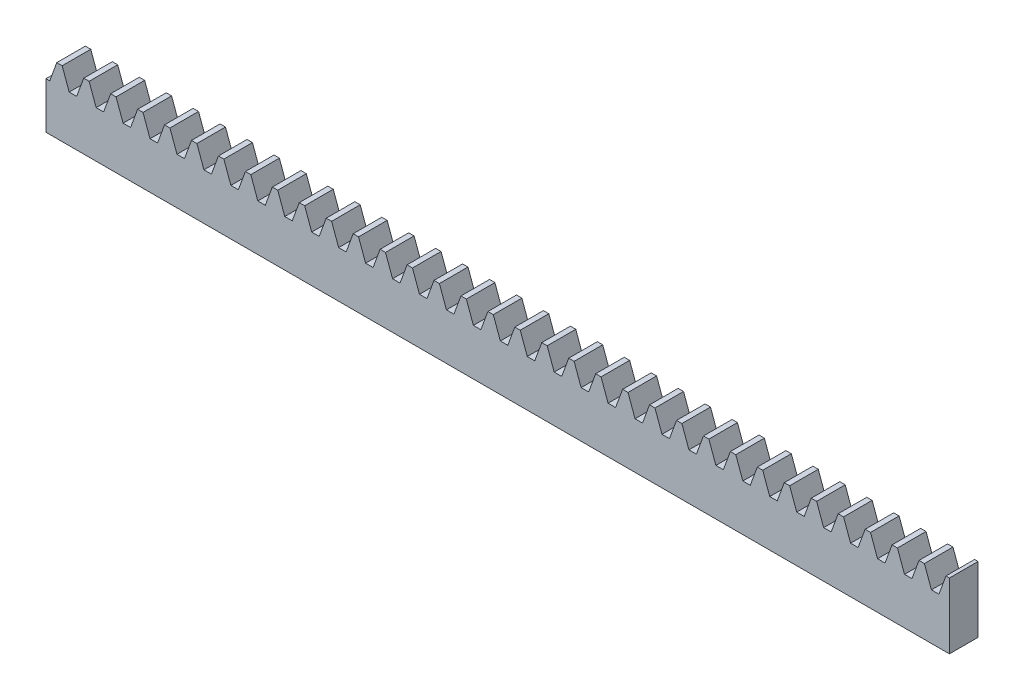
SolidWorks part; units mm, degrees
ref_plane "Plane1" through (0, 0, 0) normal (0, 0, 1) x (1, 0, 0)
ref_plane "Plane2" through (0, 0, 0) normal (0, 1, 0) x (1, 0, 0)
ref_plane "Plane3" through (0, 0, 0) normal (1, 0, 0) x (0, 0, -1)
sketch "HoldingSke" plane through (0, 0, 0) normal (0, 1, 0) x (1, 0, 0)
  line L0 (0, 0) -> (0.0928, 0.6602)
  line L1 (-15, 0) -> (100, 0) construction
  line L2 (0, 0) -> (-2.1039, 2.3779)
  line L3 (0, 0) -> (-11.863, 4.5341)
  line L4 (0, 0) -> (7.0742, 4.9534)
  line L5 (0, 0) -> (-23.7986, -8.8762)
  line L6 (0, 0) -> (-10.5278, -7.1032)
  line L9 (-71.009, 38.7566) -> (77.4625, 92.7958)
  line L10 (-76.2, 3.8779) -> (-66.2, 3.8779)
  line L11 (0, 0) -> (-5, 0)
  line L12 (-76.2, 101.6) -> (-76.147, 101.6)
  line L13 (24.9733, 27.94) -> (52.9518, 28.4284)
  line L14 (24.9733, 27.94) -> (24.9743, 27.94)
  line L15 (24.9733, 27.94) -> (100.4006, 29.5858)
  circle A0 centre (0, 0) radius 19.05
  circle A1 centre (0, 0) radius 5
  circle A2 centre (0, 0) radius 12.7
  dimension "MPH" = 10
  dimension "Diameter" = 38.1
  dimension "Num_teeth" = 35
  dimension "Pitch" = 0.6667
  dimension "Width" = 5
  dimension "Show_teeth" = 998
  dimension "Thickness" = 12.7
  dimension "Ap" = 20
  dimension "Pitch_height" = 10
  dimension "Backlash" = 0.053
  dimension "Addendum_fac" = 1
  dimension "Dedendum_fac" = 1.25
  dimension "Clearance_fac" = 0.25
  dimension "Dedendum_add" = 0.001
  dimension "Length" = 158
  dimension "Module" = 1.5
sketch "BlankSke" plane through (0, 0, 0) normal (0, 0, 1) x (1, 0, 0)
  line L1 (0, 0) -> (158, 0)
  line L2 (0, 0) -> (0, 11.5)
  line L3 (0, 11.5) -> (158, 11.5)
  line L4 (158, 0) -> (158, 11.5)
  dimension "Length" = 158
  dimension "Blank_height" = 11.5
extrude "Blank" add sketch "BlankSke" against normal blind 5
sketch "TooCutSkeIll" plane through (0, 0, 0) normal (0, 0, 1) x (1, 0, 0)
  line L0 (-1.8687, 11.4605) -> (-0.7447, 8.3724)
  line L1 (-0.3914, 8.125) -> (0.3914, 8.125)
  line L2 (0.7447, 8.3724) -> (1.8687, 11.4605)
  line L3 (158, 11.5) -> (0, 11.5) construction
  line L4 (0, 0) -> (0, 64.897) construction
  line L5 (-13.208, 10) -> (12.954, 10) construction
  line L6 (0, 0) -> (158, 0) construction
  line L7 (1.3371, 10) -> (1.3371, 48.7463) construction
  line L8 (-1.3371, 10) -> (-1.3371, 48.7463) construction
  line L9 (1.9251, 11.5) -> (1.9251, 11.5254)
  line L10 (-1.9251, 11.5) -> (-1.9251, 11.5254)
  line L11 (-1.9251, 11.5254) -> (1.9251, 11.5254)
  arc A0 (0.3914, 8.125) -> (0.7447, 8.3724) centre (0.3914, 8.501) ccw
  arc A1 (-0.7447, 8.3724) -> (-0.3914, 8.125) centre (-0.3914, 8.501) ccw
  arc A2 (1.9251, 11.5) -> (1.8687, 11.4605) centre (1.9251, 11.44) ccw
  arc A3 (-1.8687, 11.4605) -> (-1.9251, 11.5) centre (-1.9251, 11.44) ccw
  dimension "Root_fillet" = 0.376
  dimension "Break_rad" = 0.06
  dimension "Pitch_height" = 10
  dimension "Gap_width" = 2.6742
  dimension "Dedendum" = 1.875
  dimension "Addendum_plus" = 1.5254
  dimension "Pressure_angle" = 20
extrude "ToothCutIll" [suppressed] cut sketch "TooCutSkeIll" against normal through all
sketch "TooCutSkeSim" plane through (0, 0, 0) normal (0, 0, 1) x (1, 0, 0)
  line L0 (0.6547, 8.125) -> (-0.6547, 8.125)
  line L1 (1.8923, 11.5254) -> (0.6547, 8.125)
  line L2 (0, 17.4625) -> (0, 53.467) construction
  line L3 (1.8923, 11.5254) -> (-1.8923, 11.5254)
  line L6 (-1.8923, 11.5254) -> (-0.6547, 8.125)
  line L9 (-1.3371, 10) -> (1.3371, 10) construction
  line L10 (0, 0) -> (158, 0) construction
  line L11 (1.3371, 10) -> (1.3371, 53.467) construction
  line L12 (-1.3371, 10) -> (-1.3371, 53.467) construction
  dimension "Pitch_height" = 10
  dimension "Pressure_angle" = 20
  dimension "Gap_width" = 2.6742
  dimension "Dedendum" = 1.875
  dimension "Addendum_plus" = 1.5254
extrude "ToothCutSim" cut sketch "TooCutSkeSim" against normal through all
pattern_linear "TeethCuts" count 34 spacing 4.7124 along (1, 0, 0) of "ToothCutIll", "ToothCutSim"
equation "' \"Module@HoldingSke\" = 6.35"
equation "' \"Num_teeth@HoldingSke\" = 12"
equation "' \"Ap@HoldingSke\" =  20"
equation "' \"Width@HoldingSke\" = 0.25 * 25.4"
equation "' \"Show_teeth@HoldingSke\" = 500"
equation "' \"Backlash@HoldingSke\" = 0.009 * 25.4"
equation "' \"Addendum_fac@HoldingSke\" = 1.0"
equation "' \"Dedendum_fac@HoldingSke\" = 1.25"
equation "' \"Dedendum_add@HoldingSke\" = 0.00005 * 25.4"
equation "' \"Clearance_fac@HoldingSke\" = 0.25"
equation "' \"Pitch_height@HoldingSke\" = 1 * 25.4"
equation "' \"Length@HoldingSke\" = 4.71 * 25.4"
equation "\"Pitch@HoldingSke\" = 1 / \"Module@HoldingSke\""
equation "\"MPH@HoldingSke\" = \"Dedendum_fac@HoldingSke\" / \"Pitch@HoldingSke\" + 2 * \"Dedendum_add@HoldingSke\" + 0.002 * 25.4"
equation "\"MPH@HoldingSke\" = ((sgn( \"MPH@HoldingSke\" - \"Pitch_height@HoldingSke\")+1)*( \"MPH@HoldingSke\" - \"Pitch_height@HoldingSke\"))/2 + \"Pitch_height@HoldingSke\""
equation "\"Blank_height@BlankSke\" = \"Pitch_height@HoldingSke\" + \"Addendum_fac@HoldingSke\"  / \"Pitch@HoldingSke\" "
equation "\"Length@BlankSke\" =  \"Length@HoldingSke\""
equation "\"Face_width@Blank\" = \"Width@HoldingSke\""
equation "\"Pressure_angle@TooCutSkeIll\" = \"Ap@HoldingSke\""
equation "\"Addendum_plus@TooCutSkeIll\" =  \"Addendum_fac@HoldingSke\"  / \"Pitch@HoldingSke\" + 0.001 *25.4"
equation "\"Dedendum@TooCutSkeIll\" = \"Dedendum_fac@HoldingSke\"  / \"Pitch@HoldingSke\""
equation "\"Pitch_height@TooCutSkeIll\" =  \"MPH@HoldingSke\""
equation "\"Gap_width@TooCutSkeIll\" = 3.14159265 / 2 / \"Pitch@HoldingSke\" + 6 * \"Backlash@HoldingSke\""
equation "\"Pressure_angle@TooCutSkeSim\" = \"Ap@HoldingSke\""
equation "\"Addendum_plus@TooCutSkeSim\" =  \"Addendum_fac@HoldingSke\"  / \"Pitch@HoldingSke\" + 0.001 * 25.4"
equation "\"Dedendum@TooCutSkeSim\" = \"Dedendum_fac@HoldingSke\"  / \"Pitch@HoldingSke\""
equation "\"Pitch_height@TooCutSkeSim\" =  \"MPH@HoldingSke\""
equation "\"Gap_width@TooCutSkeSim\" = 3.14159265 / 2 / \"Pitch@HoldingSke\" + 6 * \"Backlash@HoldingSke\""
equation "\"Root_fillet@TooCutSkeIll\" = \"Clearance_fac@HoldingSke\" / \"Pitch@HoldingSke\" + \"Dedendum_add@HoldingSke\""
equation "\"Break_rad@TooCutSkeIll\" = 0.02 / \"Pitch@HoldingSke\" * 2"
equation "\"Linear_pitch@TeethCuts\" = 3.14159265 / \"Pitch@HoldingSke\""
equation "\"Num_teeth@HoldingSke\" = int( ( \"Length@HoldingSke\" + 0 ) / (3.14159265 / \"Pitch@HoldingSke\")) + 0.9999  + 1"
equation " \"Num_teeth@TeethCuts\" = int( \"Show_teeth@HoldingSke\" ) + 1"
equation " \"Num_teeth@TeethCuts\" = ((sgn( \"Num_teeth@TeethCuts\" - \"Num_teeth@HoldingSke\" )-1)*( \"Num_teeth@TeethCuts\" - \"Num_teeth@HoldingSke\" ))/-2+ \"Num_teeth@HoldingSke\""
equation " \"Num_teeth@TeethCuts\" = ((sgn( \"Num_teeth@TeethCuts\" - 2.0)+1)*( \"Num_teeth@TeethCuts\" - 2.0))/2 +2.0"
